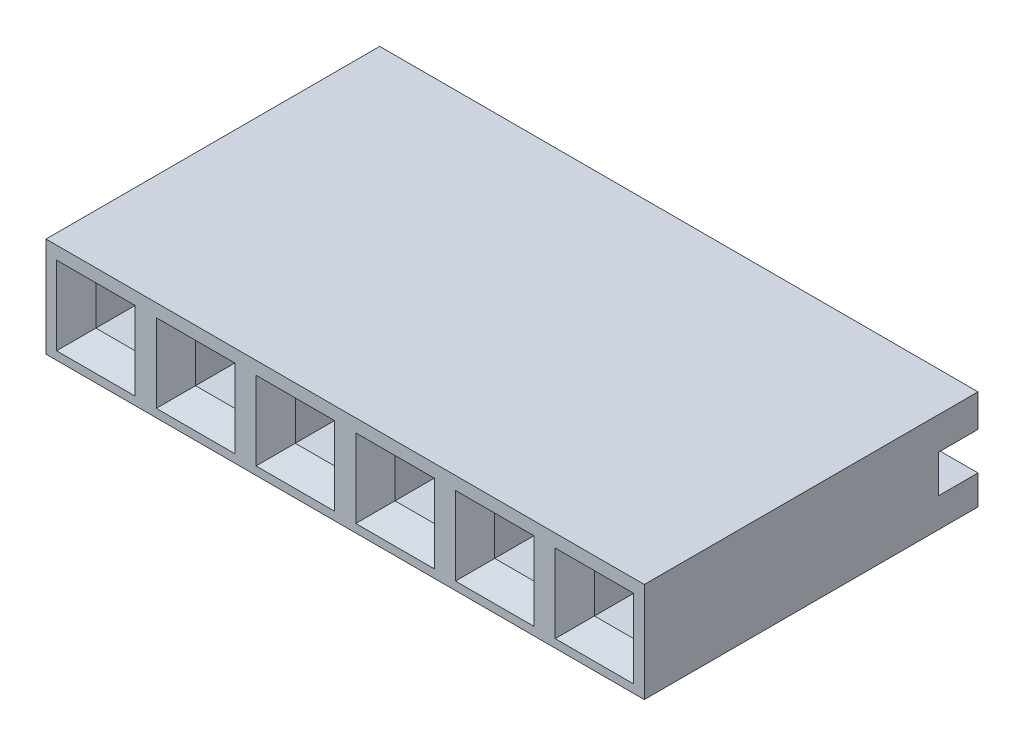
SolidWorks part; units mm, degrees
material "ABS"
ref_plane "Front Plane" through (0, 0, 0) normal (0, 0, 1) x (1, 0, 0)
ref_plane "Top Plane" through (0, 0, 0) normal (0, 1, 0) x (1, 0, 0)
ref_plane "Right Plane" through (0, 0, 0) normal (1, 0, 0) x (0, 0, -1)
sketch "Sketch1" plane through (0, 0, 0) normal (1, 0, 0) x (0, 0, -1)
  line L16 (8.5, 2.54) -> (0, 2.54)
  line L17 (0, 2.54) -> (0, 0)
  line L18 (0, 0) -> (8.5, 0)
  line L19 (8.5, 0) -> (8.5, 0.75)
  line L20 (8.5, 0.75) -> (7.5, 0.75)
  line L21 (7.5, 0.75) -> (7.5, 1.71)
  line L22 (7.5, 1.71) -> (8.5, 1.71)
  line L23 (8.5, 1.71) -> (8.5, 2.54)
  dimension "D1" = 0.83
  dimension "D2" = 0.75
  dimension "D3" = 1
  dimension "D4" = 8.5
  dimension "D5" = 2.54
extrude "Boss-Extrude1" add sketch "Sketch1" against normal blind 15.24 separate body
sketch "Sketch2" plane through (0, 0, -7.5) normal (0, 0, -1) x (-1, 0, 0)
  line L3 (2.27, 1.11) -> (2.27, 1.71)
  line L4 (2.27, 1.11) -> (0.27, 1.11)
  line L5 (0.27, 1.11) -> (0.27, 1.71)
  line L6 (2.27, 1.71) -> (0.27, 1.71)
  line L7 (15.24, 1.71) -> (0, 1.71) construction
  line L8 (0, 0.75) -> (0, 1.71) construction
  dimension "D1" = 0.6
  dimension "D2" = 0.27
  dimension "D3" = 2
extrude "Cut-Extrude1" cut sketch "Sketch2" against normal blind 5.5
sketch "Sketch3" plane through (0, 0, 0) normal (0, 0, -1) x (-1, 0, 0)
  line L4 (0.77, 1.71) -> (1.77, 1.71)
  line L5 (0.77, 0.71) -> (0.77, 1.71)
  line L6 (1.77, 0.71) -> (0.77, 0.71)
  line L7 (1.77, 1.71) -> (1.77, 0.71)
  line L8 (2.27, 1.71) -> (0.27, 1.71) construction
  line L9 (0, 0.75) -> (0, 1.71) construction
  dimension "D1" = 1
  dimension "D2" = 0.77
extrude "Cut-Extrude2" cut sketch "Sketch3" along normal blind 6
sketch "Sketch4" plane through (0, 0, 0) normal (0, 0, 1) x (1, 0, 0)
  line L8 (-2.27, 2.21) -> (-2.27, 0.21)
  line L9 (-2.27, 0.21) -> (-0.27, 0.21)
  line L10 (-0.27, 0.21) -> (-0.27, 2.21)
  line L11 (-0.27, 2.21) -> (-2.27, 2.21)
  line L12 (-2.27, 2.21) -> (-2.27, 0.21)
  line L13 (-2.27, 0.21) -> (-0.27, 0.21)
  line L14 (-0.27, 0.21) -> (-0.27, 2.21)
  line L15 (-0.27, 2.21) -> (-2.27, 2.21)
  dimension "D1" = 0.5
extrude "Cut-Extrude3" cut sketch "Sketch4" against normal blind 0.5 draft 45
pattern_linear "LPattern1" count 8 spacing 2.54 along (-1, 0, 0) of "Cut-Extrude2", "Cut-Extrude1", "Cut-Extrude3"
sketch "Sketch6" plane through (0, 0, -8.5) normal (0, 0, -1) x (-1, 0, 0)
  line L0 (15.24, 2.54) -> (0, 2.54) construction
  line L1 (15.24, 0) -> (0, 0) construction
  line L2 (15.24, 2.54) -> (0, 2.54)
  line L3 (15.24, 0) -> (0, 0)
  line L4 (15.24, 2.54) -> (0, 0) construction
  point P4 (7.62, 1.27)
